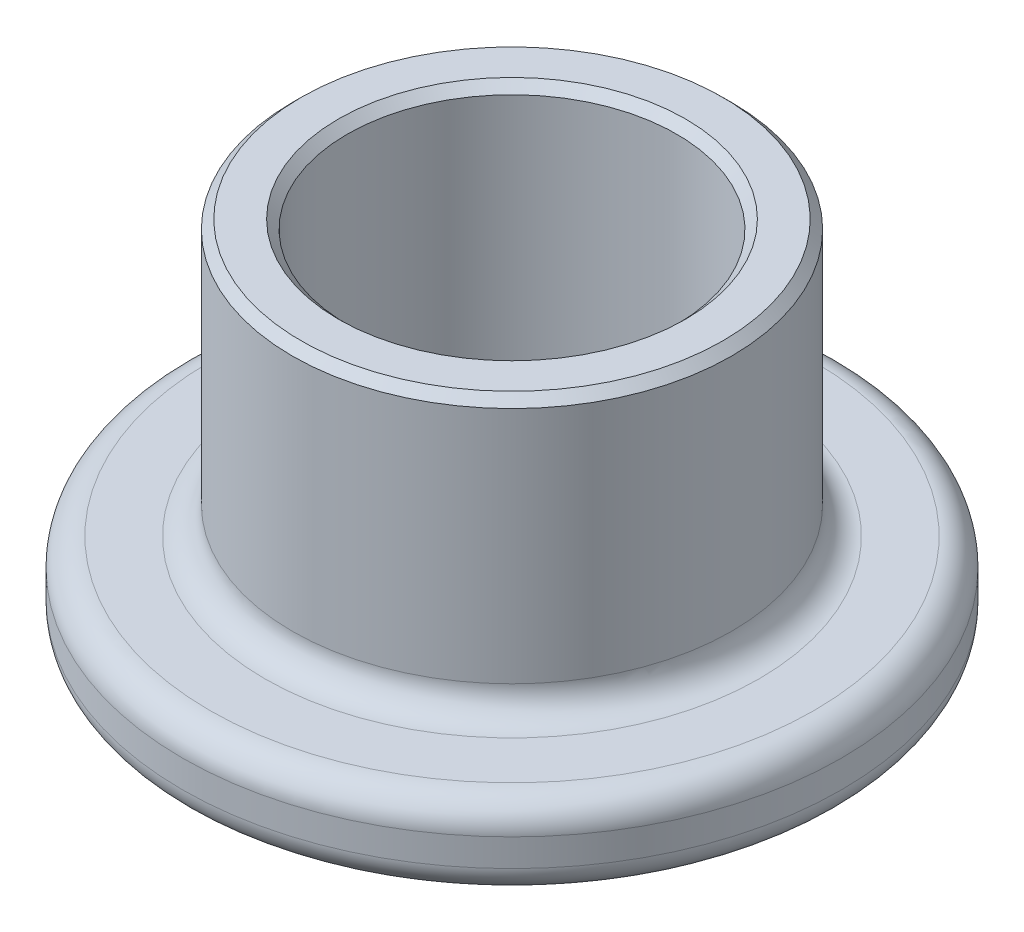
SolidWorks part; units mm, degrees
ref_plane "Front Plane" through (0, 0, 0) normal (0, 0, 1) x (1, 0, 0)
ref_plane "Top Plane" through (0, 0, 0) normal (0, 1, 0) x (1, 0, 0)
ref_plane "Right Plane" through (0, 0, 0) normal (1, 0, 0) x (0, 0, -1)
sketch "Sketch1" plane through (0, 0, 0) normal (0, 0, 1) x (1, 0, 0)
  line L0 (0, 1.8967) -> (0, -2.4436) construction
  line L1 (2.3813, 0) -> (4.7625, 0)
  line L2 (4.7625, 0) -> (4.7625, 1.1906)
  line L3 (4.7625, 1.1906) -> (3.175, 1.1906)
  line L4 (3.175, 1.1906) -> (3.175, 5.1594)
  line L5 (3.175, 5.1594) -> (2.3813, 5.1594)
  line L6 (2.3813, 0) -> (2.3813, 5.1594)
  dimension "D1" = 3.9688
  dimension "D2" = 1.1906
  dimension "D3" = 6.35
  dimension "D4" = 9.525
  dimension "D5" = 4.7625
revolve "Revolve1" add sketch "Sketch1" angle 360 about L0
fillet "Fillet1" radius 0.3969 3 edges at (-4.7625, 0, 0) (-4.7625, 1.1906, 0) (-3.175, 1.1906, 0)
chamfer "Chamfer1" distance 0.127 angle 45 3 edges at (-2.3812, 0, 0) (-3.175, 5.1594, 0) (-2.3813, 5.1594, 0)
